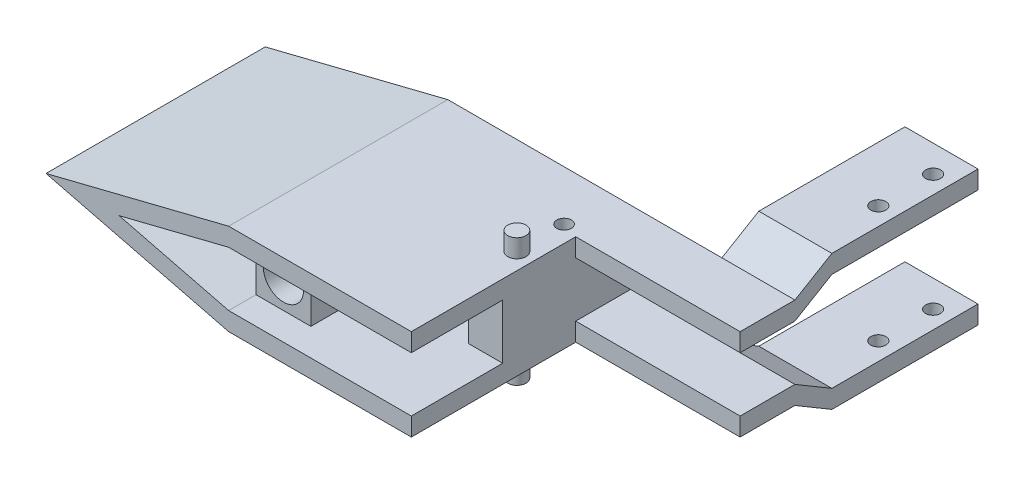
SolidWorks part; units mm, degrees
ref_plane "Plan de face" through (0, 0, 0) normal (0, 0, 1) x (1, 0, 0)
ref_plane "Plan de dessus" through (0, 0, 0) normal (0, 1, 0) x (1, 0, 0)
ref_plane "Plan de droite" through (0, 0, 0) normal (1, 0, 0) x (0, 0, -1)
sketch "Esquisse1" plane through (0, 0, 0) normal (0, 0, 1) x (1, 0, 0)
  line L0 (20.1839, 0) -> (-29.8161, 0)
  line L1 (-29.8161, 0) -> (-79.8161, -12.5)
  line L2 (-79.8161, -12.5) -> (-29.8161, -25)
  line L3 (-29.8161, -25) -> (20.1839, -25)
  line L4 (20.1839, -25) -> (20.1839, -20)
  line L5 (20.1839, -20) -> (-29.8161, -20)
  line L6 (-29.8161, -20) -> (-59.8161, -12.5)
  line L7 (-59.8161, -12.5) -> (-29.8161, -5)
  line L8 (-29.8161, -5) -> (20.1839, -5)
  line L9 (20.1839, -5) -> (20.1839, 0)
  line L15 (-43.1994, -16.6542) -> (-37.6148, -18.0503)
  point P15 (0, 0)
  point P17 (0, 0)
  dimension "D1" = 25
  dimension "D2" = 5
  dimension "D3" = 5
  dimension "D4" = 50
  dimension "D5" = 100
extrude "Boss.-Extru.1" add sketch "Esquisse1" along normal blind 60 contours L8 L9 L0 L1 L2 L3 L4 L5 L6 L7
sketch "Esquisse3" plane through (0, 0, 0) normal (0, 0, 1) x (1, 0, 0)
  line L0 (20.1839, -20) -> (-29.8161, -20) construction
  line L1 (-29.8161, -5) -> (-14.8161, -5)
  line L2 (-29.8161, -5) -> (-29.8161, -20)
  line L3 (-29.8161, -20) -> (-14.8161, -20)
  line L4 (-14.8161, -5) -> (-14.8161, -20)
  dimension "D1" = 15
extrude "Boss.-Extru.2" add sketch "Esquisse3" along normal blind 50 from offset 2.5
sketch "Esquisse4" plane through (0, 0, 0) normal (0, 0, 1) x (1, 0, 0)
  line L0 (-14.8161, -5) -> (-29.8161, -20) construction
  line L1 (-29.8161, -5) -> (-14.8161, -20) construction
  circle A0 centre (-22.3161, -12.5) radius 5.5
  dimension "D1" = 11
extrude "Enlèv. mat.-Extru.1" cut sketch "Esquisse4" along normal blind 105 from offset 10 offset against normal yes
sketch "Esquisse5" plane through (0, 0, 0) normal (0, 0, 1) x (1, 0, 0)
  line L0 (20.1839, -20) -> (-29.8161, -20) construction
  line L1 (20.1839, -5) -> (10.8559, -5)
  line L2 (20.1839, -5) -> (20.1839, -20)
  line L3 (20.1839, -20) -> (10.8559, -20)
  line L4 (10.8559, -5) -> (10.8559, -20)
extrude "Boss.-Extru.3" add sketch "Esquisse5" along normal blind 35
ref_plane "Plan1" through (0, -25, 0) normal (0, -1, 0) x (-1, 0, 0)
sketch "Esquisse12" plane through (0, 0, 0) normal (0, 1, 0) x (1, 0, 0)
  line L1 (-29.8161, 0) -> (65.1839, 0)
  line L2 (-29.8161, 0) -> (-29.8161, -15)
  line L3 (-29.8161, -15) -> (65.1839, -15)
  line L4 (65.1839, 0) -> (65.1839, -15)
  dimension "D1" = 95
  dimension "D2" = 15
extrude "Boss.-Extru.9" add sketch "Esquisse12" against normal blind 5
sketch "Esquisse13" plane through (0, -25, 0) normal (0, -1, 0) x (-1, 0, 0)
  line L1 (29.8161, 0) -> (-65.1839, 0)
  line L2 (29.8161, 0) -> (29.8161, -15)
  line L3 (29.8161, -15) -> (-65.1839, -15)
  line L4 (-65.1839, 0) -> (-65.1839, -15)
  dimension "D1" = 95
extrude "Boss.-Extru.10" add sketch "Esquisse13" against normal blind 5 contours L3 L4 L1 L2
ref_plane "Plan3" through (65.1839, 0, 0) normal (1, 0, 0) x (0, 0, -1)
sketch "Esquisse14" plane through (65.1839, 0, 0) normal (1, 0, 0) x (0, 0, -1)
  line L0 (-15, -20) -> (0, -20)
  line L1 (0, -20) -> (10.1138, -26)
  line L2 (10.1138, -26) -> (50.1138, -26)
  line L3 (50.1138, -26) -> (50.1138, -31)
  line L4 (50.1138, -31) -> (10.1138, -31)
  line L5 (10.1138, -31) -> (0, -25)
  line L6 (0, -25) -> (-15, -25)
  line L7 (-15, -20) -> (-15, -25) construction
  line L8 (-15, -25) -> (-15, -20)
  line L9 (-15.7087, -12.5) -> (42.5423, -12.5)
  line L10 (0, 0) -> (-15, 0)
  line L11 (10.1138, 6) -> (0, 0)
  line L12 (50.1138, 6) -> (10.1138, 6)
  line L13 (50.1138, 1) -> (50.1138, 6)
  line L14 (10.1138, 1) -> (50.1138, 1)
  line L15 (0, -5) -> (10.1138, 1)
  line L16 (-15, -5) -> (0, -5)
  line L17 (-15, 0) -> (-15, -5)
  dimension "D1" = 40
  dimension "D2" = 5
  dimension "D3" = 5
  dimension "D4" = 27
  dimension "D5" = 11.7596
sketch "Esquisse15" plane through (65.1839, 0, 0) normal (1, 0, 0) x (0, 0, -1)
  line L0 (-15.6261, -12.5) -> (41.3285, -12.5)
extrude "Boss.-Extru.12" add sketch "Esquisse14" against normal blind 20 contours L10 L17 L16 L15 L14 L13 L12 L11 | L8 L6 L5 L4 L3 L2 L1 L0
ref_plane "Plan4" through (0, 6, 0) normal (0, 1, 0) x (1, 0, 0)
sketch "Esquisse18" plane through (0, 6, 0) normal (0, 1, 0) x (1, 0, 0)
  circle A2 centre (60.2696, 42.7373) radius 2.05
  circle A3 centre (60.2696, 27.7373) radius 2.05
  dimension "D1" = 4.1
  dimension "D2" = 4.1
  dimension "D3" = 15
extrude "Enlèv. mat.-Extru.4" cut sketch "Esquisse18" against normal blind 50
sketch "Esquisse20" plane through (0, -25, 0) normal (0, -1, 0) x (-1, 0, 0)
  circle A0 centre (-15.6121, -13.6214) radius 2
  dimension "D1" = 4
extrude "Enlèv. mat.-Extru.6" cut sketch "Esquisse20" against normal through all
sketch "Esquisse21" plane through (0, -25, 0) normal (0, -1, 0) x (-1, 0, 0)
  circle A0 centre (-15.6121, -26.5344) radius 2.5
  dimension "D1" = 5
extrude "Boss.-Extru.13" add sketch "Esquisse21" against normal blind 35 from offset 5 contours A0
